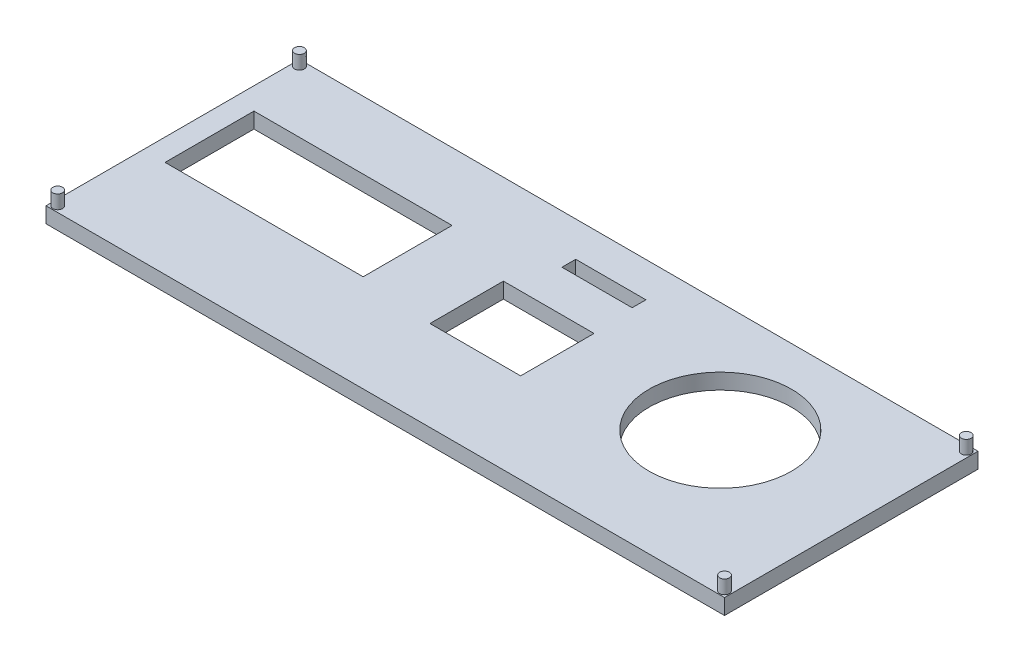
SolidWorks part; units mm, degrees
ref_plane "Front Plane" through (0, 0, 0) normal (0, 0, 1) x (1, 0, 0)
ref_plane "Top Plane" through (0, 0, 0) normal (0, 1, 0) x (1, 0, 0)
ref_plane "Right Plane" through (0, 0, 0) normal (1, 0, 0) x (0, 0, -1)
sketch "Sketch1" plane through (0, 0, 0) normal (0, 1, 0) x (1, 0, 0)
  line L1 (87, -32.5) -> (-87, -32.5)
  line L2 (87, -32.5) -> (87, 32.5)
  line L3 (87, 32.5) -> (-87, 32.5)
  line L4 (-87, -32.5) -> (-87, 32.5)
  line L5 (87, -32.5) -> (-87, 32.5) construction
  line L6 (87, 32.5) -> (-87, -32.5) construction
  point P1 (0, 0)
  dimension "D1" = 65
  dimension "D2" = 174
extrude "Boss-Extrude1" add sketch "Sketch1" along normal blind 4
sketch "Sketch2" plane through (0, 4, 0) normal (0, 1, 0) x (1, 0, 0)
  circle A0 centre (49.293, 4.12) radius 18.25
  dimension "D1" = 36.5
sketch "Sketch4" plane through (0, 4, 0) normal (0, 1, 0) x (1, 0, 0)
  line L0 (87, 32.5) -> (-87, 32.5) construction
  line L1 (-30.5703, 15.2) -> (-81.3703, 15.2)
  line L2 (-30.5703, 15.2) -> (-30.5703, -7.6)
  line L3 (-30.5703, -7.6) -> (-81.3703, -7.6)
  line L4 (-81.3703, 15.2) -> (-81.3703, -7.6)
  point P4 (-55.9703, 15.2)
  dimension "D1" = 50.8
  dimension "D2" = 22.8
  dimension "D3" = 17.3
sketch "Sketch5" plane through (0, 4, 0) normal (0, 1, 0) x (1, 0, 0)
  line L0 (87, -32.5) -> (87, 32.5) construction
  line L1 (-7.2, 20.0115) -> (10.8, 20.0115)
  line L2 (-7.2, 20.0115) -> (-7.2, 23.5429)
  line L3 (-7.2, 23.5429) -> (10.8, 23.5429)
  line L4 (10.8, 20.0115) -> (10.8, 23.5429)
  point P5 (10.8, 21.7772)
  dimension "D1" = 18
  dimension "D2" = 76.2
sketch "Sketch8" plane through (0, 4, 0) normal (0, 1, 0) x (1, 0, 0)
  point P0 (0, 0)
sketch "Sketch9" plane through (0, 4, 0) normal (0, 1, 0) x (1, 0, 0)
  line L5 (-11.6243, -9.4172) -> (11.6243, -9.4172)
  line L6 (-11.6243, -9.4172) -> (-11.6243, 9.4172)
  line L7 (-11.6243, 9.4172) -> (11.6243, 9.4172)
  line L8 (11.6243, -9.4172) -> (11.6243, 9.4172)
  line L9 (-11.6243, -9.4172) -> (11.6243, 9.4172) construction
  line L10 (-11.6243, 9.4172) -> (11.6243, -9.4172) construction
  point P0 (0, 0)
extrude "Cut-Extrude1" cut sketch "Sketch2" against normal blind 4
extrude "Cut-Extrude2" cut sketch "Sketch4" against normal blind 4
extrude "Cut-Extrude3" cut sketch "Sketch5" against normal blind 4
extrude "Cut-Extrude4" cut sketch "Sketch9" against normal blind 4
sketch "Sketch10" plane through (0, 4, 0) normal (0, 1, 0) x (1, 0, 0)
  line L0 (-87, -32.5) -> (87, -32.5) construction
  line L2 (-87, 32.5) -> (-87, -32.5) construction
  line L3 (87, 32.5) -> (-87, 32.5) construction
  circle A0 centre (-85.5, 31) radius 1.25
  circle A1 centre (-85.5, -31) radius 1.25
  point P4 (0, 0)
  point P11 (-89.5704, 31.5606)
  point P12 (-89.7049, 32.4402)
  dimension "D1" = 2.5
  dimension "D2" = 1.5
  dimension "D3" = 1.5
  dimension "D4" = 1.5
  dimension "D5" = 1.5
sketch "Sketch12" plane through (0, 4, 0) normal (0, 1, 0) x (1, 0, 0)
  line L0 (87, -32.5) -> (87, 32.5) construction
  line L1 (87, 32.5) -> (-87, 32.5) construction
  line L2 (-87, -32.5) -> (87, -32.5) construction
  circle A0 centre (85.5, 31) radius 1.25
  circle A1 centre (85.5, -31) radius 1.25
  dimension "D2" = 2.5
  dimension "D4" = 2.5
  dimension "D5" = 1.5
  dimension "D6" = 1.5
  dimension "D1" = 1.5
  dimension "D3" = 1.5
extrude "Boss-Extrude2" add sketch "Sketch10" along normal blind 3.5
extrude "Boss-Extrude3" add sketch "Sketch12" along normal blind 3.5
